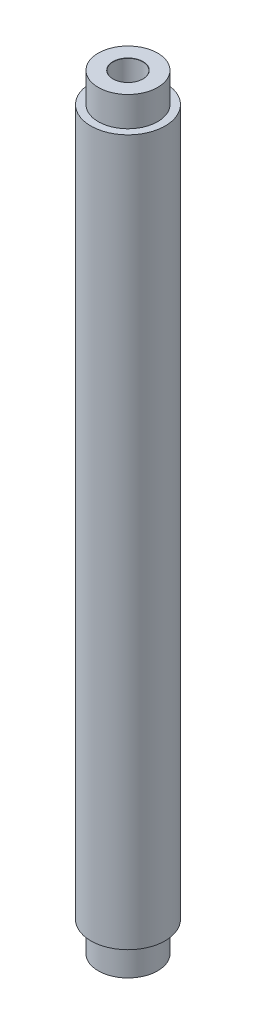
SolidWorks part; units mm, degrees
material "6061-T4 (SS)"
ref_plane "Front Plane" through (0, 0, 0) normal (0, 0, 1) x (1, 0, 0)
ref_plane "Top Plane" through (0, 0, 0) normal (0, 1, 0) x (1, 0, 0)
ref_plane "Right Plane" through (0, 0, 0) normal (1, 0, 0) x (0, 0, -1)
sketch "Sketch1" plane through (0, 0, 0) normal (0, 1, 0) x (1, 0, 0)
  circle A0 centre (0, 0) radius 5
  dimension "D1" = 10
extrude "Boss-Extrude1" add sketch "Sketch1" along normal blind 103
hole_wizard "Ø4.0mm Dowel Hole1" positions "3DSketch1" profile "Sketch4" hole size "Ø4.0" standard "ANSI Metric"
sketch3d "3DSketch1"
  line L0 (0, 103, 0) -> (0, 0, 0) construction
  point P0 (0, 103, 0)
  point P5 (0, 0, 0)
sketch "Sketch4" plane through (0, 103, 0) normal (1, 0, 0) x (0, 0, 1)
  line L0 (0, 0) -> (0, 19.2017)
  line L1 (0, 19.2017) -> (2, 18)
  line L2 (2, 18) -> (2, 0.025)
  line L3 (2, 0.025) -> (2.025, 0)
  line L5 (2.025, 0) -> (0, 0)
  line L6 (-2, 0.025) -> (-2.025, 0) construction
  line L10 (0, 19.2017) -> (-2, 18) construction
  line L11 (0, -6.35) -> (0, 107.95) construction
  dimension "Hole Dia." = 4
  dimension "Hole Depth" = 18
  dimension "Near C'Sink Dia." = 4.05
  dimension "Near C'Sink Angle" = 90
  dimension "Drill Angle" = 118
cosmetic thread "Cosmetic Thread1" parameters "D1"=15, "D2"=5
ref_plane "Plane3" through (0, 51.5, 0) normal (0, 1, 0) x (1, 0, 0)
mirror "Mirror1" about plane through (0, 51.5, 0) normal (0, 1, 0) of "Ø4.0mm Dowel Hole1"
cosmetic thread "Cosmetic Thread2" parameters "D1"=15, "D2"=5
sketch "Sketch5" plane through (0, 0, 0) normal (0, 0, 1) x (1, 0, 0)
  line L0 (0, 51.5) -> (-5, 51.5) construction
  line L1 (-5, 103) -> (-4, 103)
  line L2 (-5, 103) -> (-5, 99)
  line L3 (-5, 99) -> (-4, 99)
  line L4 (-4, 103) -> (-4, 99)
  line L9 (4.4, 51.5) -> (-4.4, 51.5) construction
  line L10 (-5, 103) -> (-5, 0) construction
  line L11 (-4, 0) -> (-4, 4)
  line L12 (-5, 4) -> (-4, 4)
  line L13 (-5, 0) -> (-5, 4)
  line L14 (-5, 0) -> (-4, 0)
  line L15 (0, 103) -> (0, 0) construction
  line L16 (5, 103) -> (-5, 103) construction
  dimension "D1" = 4
  dimension "D2" = 4
revolve "Cut-Revolve2" cut sketch "Sketch5" angle 360 about L15
equation "\"D1@Boss-Extrude1\"=103"
